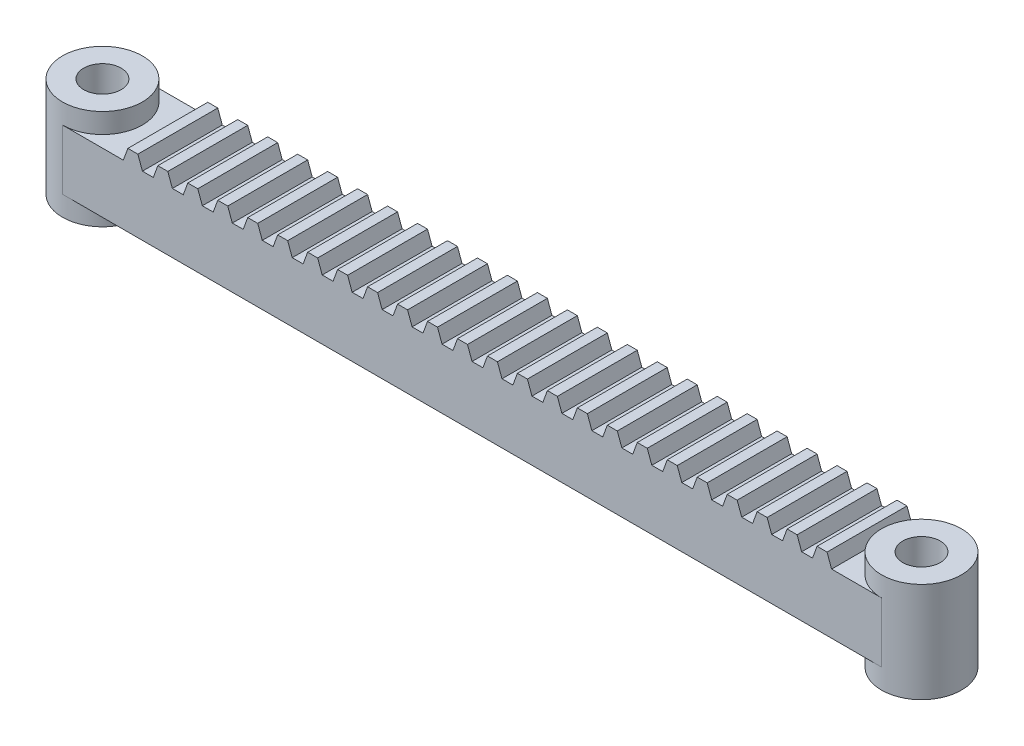
SolidWorks part; units mm, degrees
material "Galvanized Steel"
ref_plane "Front Plane" through (0, 0, 0) normal (0, 0, 1) x (1, 0, 0)
ref_plane "Top Plane" through (0, 0, 0) normal (0, 1, 0) x (1, 0, 0)
ref_plane "Right Plane" through (0, 0, 0) normal (1, 0, 0) x (0, 0, -1)
sketch "Sketch1" plane through (0, 0, 0) normal (0, 1, 0) x (1, 0, 0)
  line L1 (-82, -8) -> (82, -8)
  line L2 (-82, -8) -> (-82, 8)
  line L3 (-82, 8) -> (82, 8)
  line L4 (82, -8) -> (82, 8)
  line L5 (-82, -8) -> (82, 8) construction
  line L6 (-82, 8) -> (82, -8) construction
  point P0 (0, 0)
  dimension "D1" = 164
  dimension "D2" = 16
extrude "Boss-Extrude1" add sketch "Sketch1" along normal blind 12
sketch "Sketch2" plane through (0, 12, 0) normal (0, 1, 0) x (1, 0, 0)
  line L0 (-82, 8) -> (-82, -8) construction
  line L1 (82, -8) -> (82, 8) construction
  circle A0 centre (-82, 0) radius 8
  circle A1 centre (82, 0) radius 8
extrude "Boss-Extrude2" add sketch "Sketch2" along normal blind 4 and the other way blind 16
sketch "Sketch3" plane through (0, 0, 8) normal (0, 0, 1) x (1, 0, 0)
  line L0 (68.1801, 12) -> (72, 12)
  line L1 (-82, 12) -> (82, 12) construction
  line L2 (72, 12) -> (71.0901, 14.5)
  line L3 (71.0901, 14.5) -> (69.0901, 14.5)
  line L4 (69.0901, 14.5) -> (68.1801, 12)
  line L5 (90, -4) -> (90, 16) construction
  dimension "D1" = 18
  dimension "D2" = 2
  dimension "D3" = 40
  dimension "D4" = 2.5
extrude "Boss-Extrude3" add sketch "Sketch3" against normal blind 16
pattern_linear "LPattern1" count 24 spacing 6 along (-1, 0, 0) of "Boss-Extrude3"
sketch "Sketch4" plane through (0, 0, 0) normal (0, -1, 0) x (1, 0, 0)
  circle A0 centre (-82, 0) radius 3.75
  circle A1 centre (82, 0) radius 3.75
  dimension "D1" = 7.5
extrude "Cut-Extrude1" cut sketch "Sketch4" against normal through all both and the other way through all
